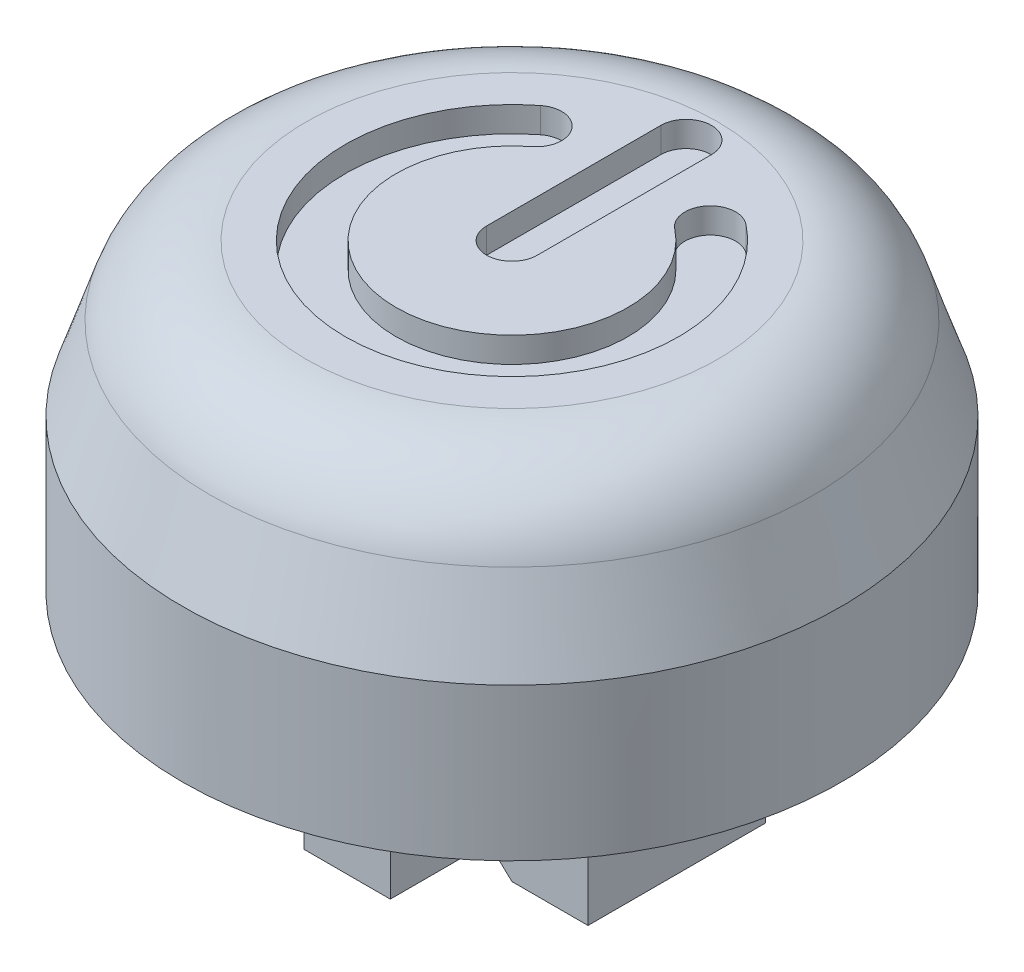
SolidWorks part; units mm, degrees
ref_plane "Front Plane" through (0, 0, 0) normal (0, 0, 1) x (1, 0, 0)
ref_plane "Top Plane" through (0, 0, 0) normal (0, 1, 0) x (1, 0, 0)
ref_plane "Right Plane" through (0, 0, 0) normal (1, 0, 0) x (0, 0, -1)
sketch "Sketch1" plane through (0, 0, 0) normal (0, 1, 0) x (1, 0, 0)
  circle A0 centre (0, 0) radius 6.5
  dimension "D1" = 13
extrude "Boss-Extrude1" add sketch "Sketch1" along normal blind 3
ref_plane "Button Top Plane" through (0, 6, 0) normal (0, 1, 0) x (1, 0, 0)
sketch "Sketch2" plane through (0, 6, 0) normal (0, 1, 0) x (1, 0, 0)
  circle A2 centre (0, 0) radius 5.5
  circle A3 centre (0, 0) radius 5.5
  dimension "D1" = 1
loft "Loft1" add profiles "Sketch2" section "Sketch2" section face at (0, 3, 6.5)
fillet "Fillet1" radius 2 1 edges at (0, 6, 5.5)
sketch "Sketch3" plane through (0, 6, 0) normal (0, 1, 0) x (1, 0, 0)
  line L0 (0, 0) -> (0, 3.435) construction
  line L1 (-0.5, 0) -> (-0.5, 3.435)
  line L2 (0.5, 0) -> (0.5, 3.435)
  line L3 (-1.716, 2.1964) -> (1.716, 2.1964) construction
  line L4 (-2.0238, 2.5904) -> (-1.4082, 1.8024) construction
  line L5 (-0.5, 3.435) -> (0.5, 3.435) construction
  arc A0 (-0.5, 0) -> (0.5, 0) centre (0, 0) ccw
  arc A1 (0.5, 3.435) -> (-0.5, 3.435) centre (0, 3.435) ccw
  arc A2 (-1.716, 2.1964) -> (1.716, 2.1964) centre (0, 0) ccw construction
  circle A3 centre (-1.716, 2.1964) radius 0.5
  circle A4 centre (1.716, 2.1964) radius 0.5
  arc A5 (-1.4082, 1.8024) -> (1.4082, 1.8024) centre (0, 0) ccw
  arc A6 (-2.0238, 2.5904) -> (2.0238, 2.5904) centre (0, 0) ccw
  point P3 (0, 1.7175)
  dimension "D1" = 1
  dimension "D2" = 3.435
  dimension "D3" = 3.432
  dimension "D4" = 38
extrude "Cut-Extrude1" cut sketch "Sketch3" against normal blind 0.5 contours L2 A1 L1 A0 | A3 A6 A4 A5 | A4 | A3
sketch "Sketch4" plane through (0, 0, 0) normal (0, -1, 0) x (1, 0, 0)
  circle A2 centre (0, 0) radius 5
  circle A3 centre (0, 0) radius 5
  dimension "D1" = 1.5
extrude "Cut-Extrude2" cut sketch "Sketch4" against normal blind 1.8
sketch "Sketch5" plane through (0, 1.8, 0) normal (0, -1, 0) x (1, 0, 0)
  line L0 (1.75, 1.75) -> (-1.75, -1.75) construction
  line L1 (1.75, 1.75) -> (-1.75, 1.75)
  line L2 (1.75, 1.75) -> (1.75, -1.75)
  line L3 (1.75, -1.75) -> (-1.75, -1.75)
  line L4 (-1.75, 1.75) -> (-1.75, -1.75)
  line L5 (3.25, 3.25) -> (3.25, -3.25)
  line L6 (3.25, -3.25) -> (-3.25, -3.25)
  line L7 (-3.25, 3.25) -> (-3.25, -3.25)
  line L8 (3.25, 3.25) -> (-3.25, 3.25)
  line L9 (3.25, 0) -> (-3.25, 0) construction
  line L10 (3.25, -3.25) -> (0.85, -3.25)
  line L11 (3.25, -3.25) -> (3.25, -1.75)
  line L12 (3.25, -1.75) -> (0.85, -1.75)
  line L13 (0.85, -3.25) -> (0.85, -1.75)
  line L14 (-3.25, -3.25) -> (-0.85, -3.25)
  line L15 (-3.25, -3.25) -> (-3.25, -1.75)
  line L16 (-3.25, -1.75) -> (-0.85, -1.75)
  line L17 (-0.85, -3.25) -> (-0.85, -1.75)
  line L18 (-3.25, 1.75) -> (-0.85, 1.75)
  line L19 (-0.85, 3.25) -> (-0.85, 1.75)
  line L20 (-3.25, 3.25) -> (-0.85, 3.25)
  line L21 (-3.25, 3.25) -> (-3.25, 1.75)
  line L22 (3.25, 1.75) -> (0.85, 1.75)
  line L23 (0.85, 3.25) -> (0.85, 1.75)
  line L24 (3.25, 3.25) -> (0.85, 3.25)
  line L25 (3.25, 3.25) -> (3.25, 1.75)
  point P23 (0, 0)
  dimension "D1" = 3.5
  dimension "D3" = 0.9
  dimension "D2" = 1.5
extrude "Boss-Extrude3" add sketch "Sketch5" along normal blind 5 contours L5 L22 L2 L12 | L17 L6 L13 L3 | L18 L7 L16 L4 | L23 L8 L19 L1
sketch "Sketch6" plane through (0, 0, 1.75) normal (0, 0, 1) x (1, 0, 0)
  line L0 (1.75, -3.2) -> (1, -2.5)
  line L2 (1.75, -3.2) -> (1.75, 1.8) construction
  line L3 (1.75, -2.5) -> (1.75, -3.2)
  line L4 (1, -2.5) -> (1.75, -2.5)
  dimension "D1" = 0.7
  dimension "D2" = 0.75
extrude "Boss-Extrude4" add sketch "Sketch6" against normal up to surface (3.5 mm away) up to face at (2.5, -0.7, -1.75)
mirror "Mirror1" about plane through (0, 0, 0) normal (1, 0, 0) of "Boss-Extrude4"
fillet "Fillet2" radius 1 4 edges at (0, 1.8, 3.25) (0, 1.8, -3.25) (-3.25, 1.8, 0) (3.25, 1.8, 0)
